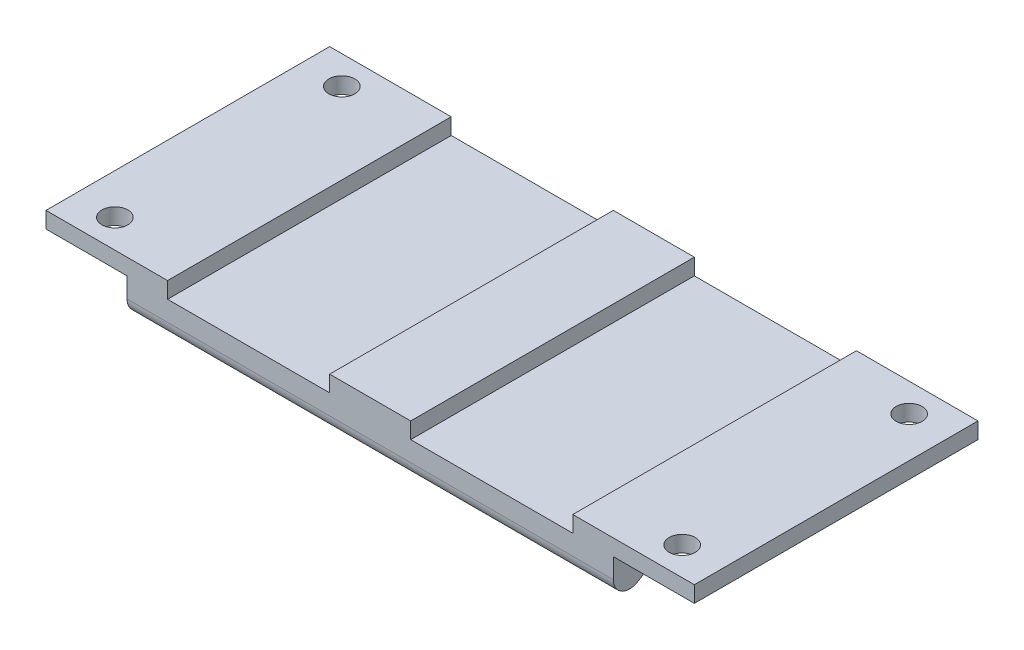
SolidWorks part; units mm, degrees
material "PEI"
ref_plane "Front Plane" through (0, 0, 0) normal (0, 0, 1) x (1, 0, 0)
ref_plane "Top Plane" through (0, 0, 0) normal (0, 1, 0) x (1, 0, 0)
ref_plane "Right Plane" through (0, 0, 0) normal (1, 0, 0) x (0, 0, -1)
sketch "Sketch1" plane through (0, 0, 0) normal (0, 1, 0) x (1, 0, 0)
  line L1 (30, -17.5) -> (-30, -17.5)
  line L2 (30, -17.5) -> (30, 17.5)
  line L3 (30, 17.5) -> (-30, 17.5)
  line L4 (-30, -17.5) -> (-30, 17.5)
  line L5 (30, -17.5) -> (-30, 17.5) construction
  line L6 (30, 17.5) -> (-30, -17.5) construction
  point P0 (0, 0)
  dimension "D1" = 35
  dimension "D2" = 60
extrude "Boss-Extrude1" add sketch "Sketch1" against normal blind 8
sketch "Sketch2" plane through (30, 0, 0) normal (1, 0, 0) x (0, 0, -1)
  line L0 (-17.5, -8) -> (-12.5, -5)
  line L1 (-12.5, -5) -> (12.5, -5)
  line L2 (0, -5) -> (0, -8)
  line L3 (17.5, -8) -> (12.5, -5)
  line L4 (17.5, 0) -> (-17.5, 0)
  line L5 (-17.5, 0) -> (-17.5, -8)
  line L6 (-17.5, -8) -> (17.5, -8)
  line L7 (17.5, -8) -> (17.5, 0)
  line L8 (17.5, 0) -> (-17.5, 0)
  line L9 (-17.5, 0) -> (-17.5, -8)
  line L10 (-17.5, -8) -> (17.5, -8)
  line L11 (17.5, -8) -> (17.5, 0)
  line M7 (-17.5, -8) -> (17.5, -8)
  dimension "D2" = 5
  dimension "D3" = 3
  dimension "D1" = 0
extrude "Cut-Extrude1" cut sketch "Sketch2" against normal through all and the other way through all contours L2 L1 L0 M7 | L3 L1 L2 M7
fillet "Fillet1" radius 2 4 edges at (0, -5, 12.5) (0, -5, -12.5) (0, -8, -17.5) (0, -8, 17.5)
sketch "Sketch3" plane through (0, 0, 17.5) normal (0, 0, 1) x (1, 0, 0)
  line L0 (-30, 0) -> (30, 0) construction
  line L1 (-25, 2) -> (-5, 2)
  line L2 (-25, 2) -> (-25, -2)
  line L3 (-25, -2) -> (-5, -2)
  line L4 (-30, 0) -> (-30, -4.4676)
  line L5 (-30, -4.4676) -> (30, -4.4676)
  line L6 (30, -4.4676) -> (30, 0)
  line L7 (30, 0) -> (-30, 0)
  line L8 (-30, 0) -> (-30, -4.4676)
  line L9 (-30, -4.4676) -> (30, -4.4676)
  line L10 (30, -4.4676) -> (30, 0)
  line L11 (30, 0) -> (-30, 0)
  line L12 (-5, 2) -> (-5, -2)
  line L13 (-25, 2) -> (-5, -2) construction
  line L14 (-25, -2) -> (-5, 2) construction
  line L15 (0, 0) -> (0, -4.4676)
  line L16 (25, -2) -> (5, 2) construction
  line L17 (25, 2) -> (5, -2) construction
  line L18 (5, 2) -> (5, -2)
  line L19 (25, -2) -> (5, -2)
  line L20 (25, 2) -> (25, -2)
  line L21 (25, 2) -> (5, 2)
  point P2 (-15, 0)
  point P13 (0, 0)
  point P18 (15, 0)
  dimension "D2" = 20
  dimension "D3" = 4
  dimension "D4" = 15
  dimension "D1" = 0
extrude "Cut-Extrude2" cut sketch "Sketch3" against normal through all contours L12 L11 L2 L3 | L20 L11 L18 L19
sketch "Sketch5" plane through (-30, 0, 0) normal (-1, 0, 0) x (0, 0, 1)
  line L1 (-17.5, 0) -> (17.5, 0)
  line L2 (-17.5, 0) -> (-17.5, -2)
  line L3 (-17.5, -2) -> (17.5, -2)
  line L4 (17.5, 0) -> (17.5, -2)
  line L6 (-17.5, 0) -> (-17.5, -4.4676)
  line L7 (-14.471, -6.1826) -> (-12.975, -5.285)
  line L8 (-11.946, -5) -> (11.946, -5)
  line L9 (12.975, -5.285) -> (14.471, -6.1826)
  line L10 (17.5, -4.4676) -> (17.5, 0)
  line L11 (17.5, 0) -> (-17.5, 0)
  line L12 (-17.5, 0) -> (-17.5, -4.4676)
  line L13 (-14.471, -6.1826) -> (-12.975, -5.285)
  line L14 (-11.946, -5) -> (11.946, -5)
  line L15 (12.975, -5.285) -> (14.471, -6.1826)
  line L16 (17.5, -4.4676) -> (17.5, 0)
  line L17 (17.5, 0) -> (-17.5, 0)
  arc A4 (-17.5, -4.4676) -> (-14.471, -6.1826) centre (-15.5, -4.4676) ccw
  arc A5 (-11.946, -5) -> (-12.975, -5.285) centre (-11.946, -7) ccw
  arc A6 (12.975, -5.285) -> (11.946, -5) centre (11.946, -7) ccw
  arc A7 (14.471, -6.1826) -> (17.5, -4.4676) centre (15.5, -4.4676) ccw
  arc A8 (-17.5, -4.4676) -> (-14.471, -6.1826) centre (-15.5, -4.4676) ccw
  arc A9 (-11.946, -5) -> (-12.975, -5.285) centre (-11.946, -7) ccw
  arc A10 (12.975, -5.285) -> (11.946, -5) centre (11.946, -7) ccw
  arc A11 (14.471, -6.1826) -> (17.5, -4.4676) centre (15.5, -4.4676) ccw
  line M13 (-17.5, 0) -> (-17.5, -4.4676)
  line M21 (17.5, -4.4676) -> (17.5, 0)
  line M22 (17.5, 0) -> (-17.5, 0)
  dimension "D2" = 2
  dimension "D1" = 0
extrude "Boss-Extrude2" add sketch "Sketch5" along normal blind 10 contours L3 M13 M21 M22
mirror "Mirror1" about plane through (0, 0, 0) normal (1, 0, 0) of "Boss-Extrude2"
sketch "Sketch6" plane through (0, 0, 0) normal (0, 1, 0) x (1, 0, 0)
  line L0 (0, 0) -> (0, 14)
  line L1 (0, 14) -> (-35, 14)
  line L2 (0, 0) -> (-40, 0)
  line L4 (-25, -17.5) -> (-25, 17.5)
  line L5 (-25, 17.5) -> (-40, 17.5)
  line L6 (-40, 17.5) -> (-40, -17.5)
  line L7 (-40, -17.5) -> (-25, -17.5)
  line L8 (-25, -17.5) -> (-25, 17.5)
  line L9 (-25, 17.5) -> (-40, 17.5)
  line L10 (-40, 17.5) -> (-40, -17.5)
  line L11 (-40, -17.5) -> (-25, -17.5)
  line L12 (-25, -17.5) -> (-5, -17.5)
  line L13 (-5, -17.5) -> (-5, 17.5)
  line L14 (-5, 17.5) -> (-25, 17.5)
  line L15 (-25, 17.5) -> (-25, -17.5)
  line L16 (-25, -17.5) -> (-5, -17.5)
  line L17 (-5, -17.5) -> (-5, 17.5)
  line L18 (-5, 17.5) -> (-25, 17.5)
  line L19 (-25, 17.5) -> (-25, -17.5)
  line L20 (5, 17.5) -> (-5, 17.5)
  line L21 (-5, 17.5) -> (-5, -17.5)
  line L22 (-5, -17.5) -> (5, -17.5)
  line L23 (5, -17.5) -> (5, 17.5)
  line L24 (5, 17.5) -> (-5, 17.5)
  line L25 (-5, 17.5) -> (-5, -17.5)
  line L26 (-5, -17.5) -> (5, -17.5)
  line L27 (5, -17.5) -> (5, 17.5)
  line L28 (5, -17.5) -> (25, -17.5)
  line L29 (25, -17.5) -> (25, 17.5)
  line L30 (25, 17.5) -> (5, 17.5)
  line L31 (5, 17.5) -> (5, -17.5)
  line L32 (5, -17.5) -> (25, -17.5)
  line L33 (25, -17.5) -> (25, 17.5)
  line L34 (25, 17.5) -> (5, 17.5)
  line L35 (5, 17.5) -> (5, -17.5)
  line L36 (40, 17.5) -> (25, 17.5)
  line L37 (25, 17.5) -> (25, -17.5)
  line L38 (25, -17.5) -> (40, -17.5)
  line L39 (40, -17.5) -> (40, 17.5)
  line L40 (40, 17.5) -> (25, 17.5)
  line L41 (25, 17.5) -> (25, -17.5)
  line L42 (25, -17.5) -> (40, -17.5)
  line L43 (40, -17.5) -> (40, 17.5)
  circle A0 centre (-35, 14) radius 1.6
  circle A1 centre (35, 14) radius 1.6
  circle A2 centre (35, -14) radius 1.6
  circle A3 centre (-35, -14) radius 1.6
  dimension "D8" = 3.2
  dimension "D6" = 14
  dimension "D7" = 35
  dimension "D1" = 0
  dimension "D2" = 0
  dimension "D3" = 0
  dimension "D4" = 0
  dimension "D5" = 0
extrude "Cut-Extrude3" cut sketch "Sketch6" against normal blind 10
